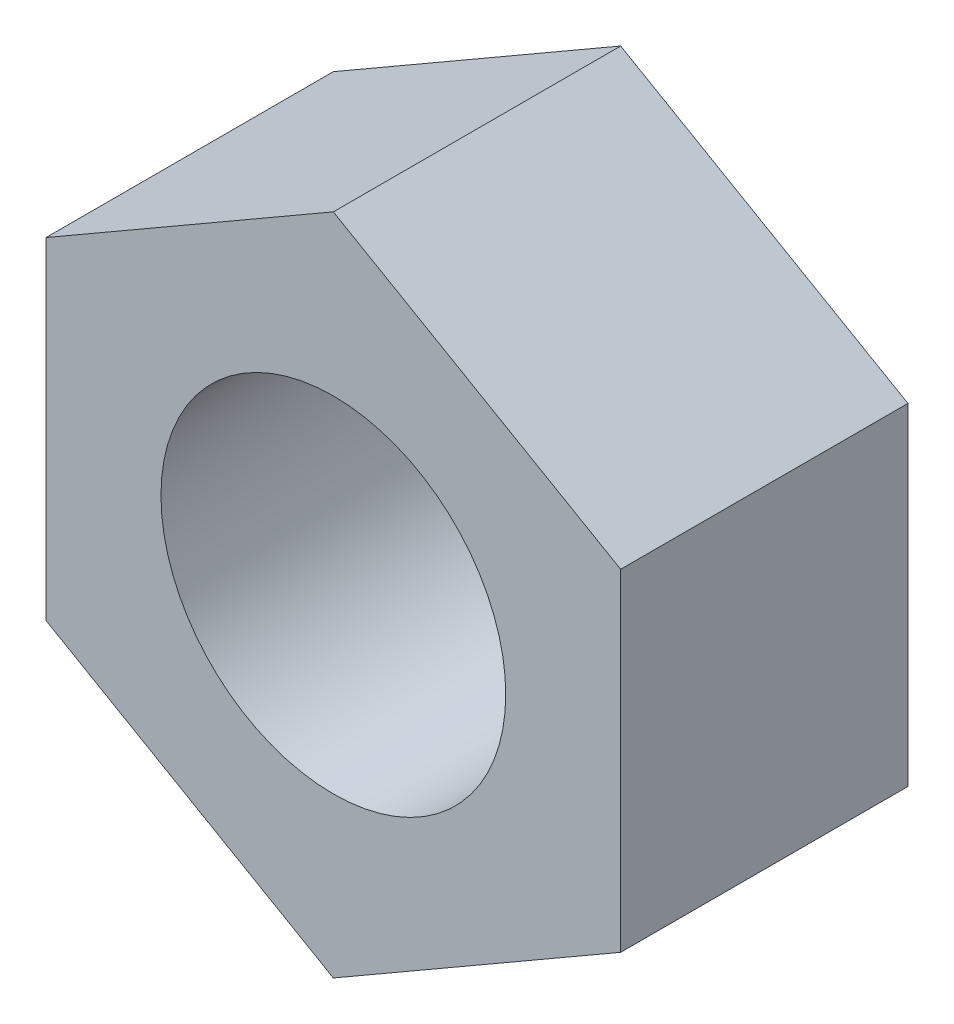
SolidWorks part; units mm, degrees
material "AISI 304"
ref_plane "前基準面" through (0, 0, 0) normal (0, 0, 1) x (1, 0, 0)
ref_plane "上基準面" through (0, 0, 0) normal (0, 1, 0) x (1, 0, 0)
ref_plane "右基準面" through (0, 0, 0) normal (1, 0, 0) x (0, 0, -1)
sketch "草圖1" plane through (0, 0, 0) normal (0, 0, 1) x (1, 0, 0)
  line L1 (0, -5.7735) -> (5, -2.8868)
  line L2 (5, -2.8868) -> (5, 2.8868)
  line L3 (5, 2.8868) -> (0, 5.7735)
  line L4 (0, 5.7735) -> (-5, 2.8868)
  line L5 (-5, 2.8868) -> (-5, -2.8868)
  line L6 (-5, -2.8868) -> (0, -5.7735)
  circle A0 centre (0, 0) radius 5 construction
  dimension "D1" = 10
extrude "伸長1" add sketch "草圖1" along normal blind 5
hole_wizard "M6x1.0 螺紋孔1" positions "草圖3" profile "草圖2" tap size "M6x1.0" standard "JIS"
sketch "草圖3" plane through (0, 0, 5) normal (0, 0, 1) x (1, 0, 0)
  point P0 (0, 0)
sketch "草圖2" plane through (0, 0, 5) normal (1, 0, 0) x (0, -1, 0)
  line L0 (0, 0) -> (0, 18.5022)
  line L1 (0, 18.5022) -> (2.5, 17)
  line L2 (2.5, 17) -> (2.5, 12)
  line L3 (2.5, 12) -> (3, 12)
  line L4 (3, 12) -> (3, 0)
  line L5 (3, 0) -> (0, 0)
  line L10 (0, 18.5022) -> (-2.5, 17) construction
  line L11 (0, -6.35) -> (0, 107.95) construction
  dimension "螺孔鑽直徑" = 5
  dimension "螺孔鑽深度" = 17
  dimension "螺紋主直徑" = 6
  dimension "螺紋深度" = 12
  dimension "導頭角度" = 118
